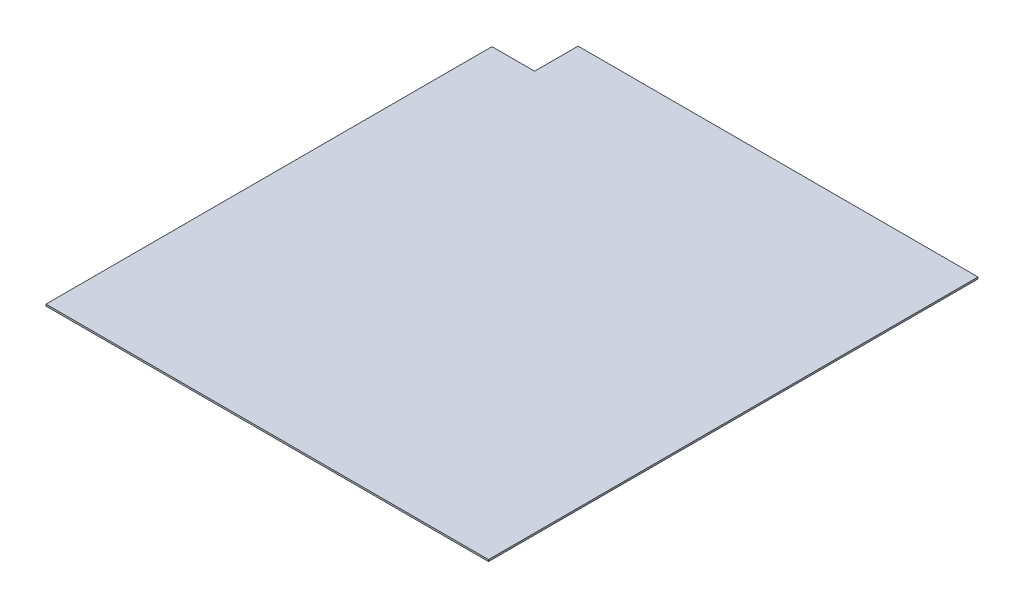
SolidWorks part; units mm, degrees
material "Polyurethane Foam Rigid"
ref_plane "Front Plane" through (0, 0, 0) normal (0, 0, 1) x (1, 0, 0)
ref_plane "Top Plane" through (0, 0, 0) normal (0, 1, 0) x (1, 0, 0)
ref_plane "Right Plane" through (0, 0, 0) normal (1, 0, 0) x (0, 0, -1)
sketch "Sketch1" plane through (0, 0, 0) normal (0, 1, 0) x (1, 0, 0)
  line L1 (0, 0) -> (1616.075, 0)
  line L2 (0, 0) -> (0, 1625.6)
  line L3 (158.75, 1787.525) -> (1616.075, 1787.525)
  line L4 (1616.075, 0) -> (1616.075, 1787.525)
  line L5 (3.175, 1628.775) -> (152.4, 1628.775)
  line L8 (155.575, 1631.95) -> (155.575, 1784.35)
  arc A0 (155.575, 1784.35) -> (158.75, 1787.525) centre (158.75, 1784.35) cw
  arc A1 (155.575, 1631.95) -> (152.4, 1628.775) centre (152.4, 1631.95) cw
  arc A2 (3.175, 1628.775) -> (0, 1625.6) centre (3.175, 1625.6) ccw
  point P9 (155.575, 1787.525)
  point P12 (155.575, 1628.775)
  point P15 (0, 1628.775)
  dimension "D5" = 3.175
  dimension "D1" = 1628.775
  dimension "D2" = 155.575
  dimension "D3" = 158.75
  dimension "D4" = 1616.075
extrude "Boss-Extrude1" add sketch "Sketch1" along normal blind 6.35
